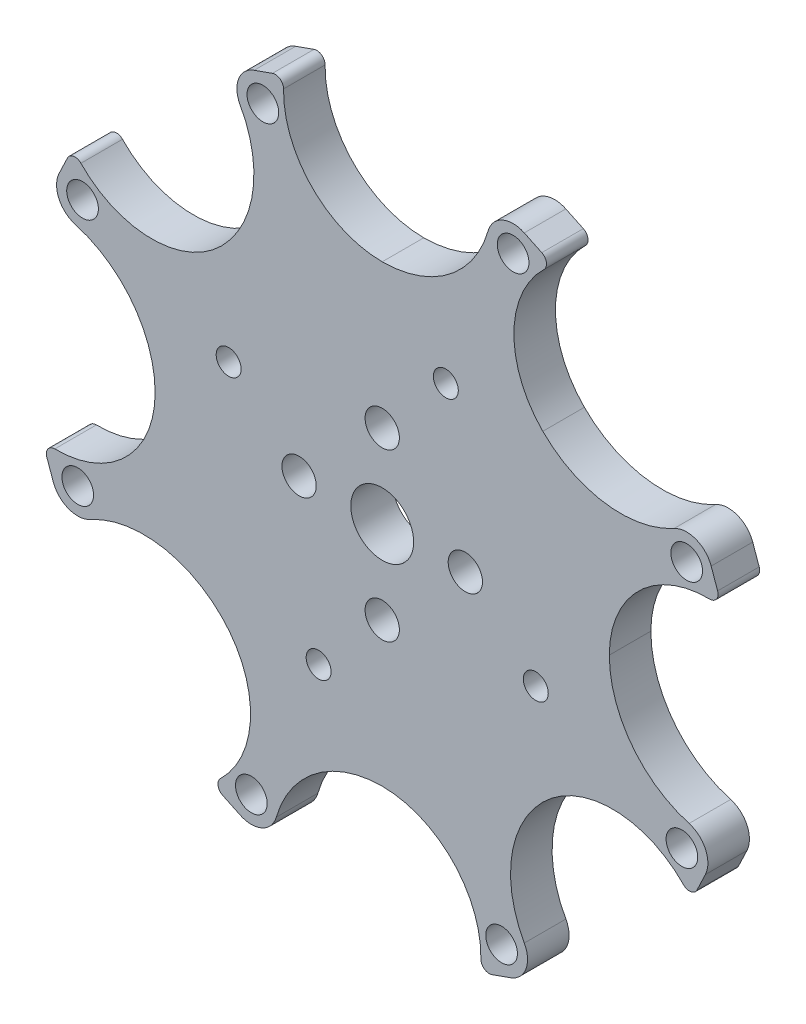
SolidWorks part; units mm, degrees
material "Thornel Mat VMA"
ref_plane "前视基准面" through (0, 0, 0) normal (0, 0, 1) x (1, 0, 0)
ref_plane "上视基准面" through (0, 0, 0) normal (0, 1, 0) x (1, 0, 0)
ref_plane "右视基准面" through (0, 0, 0) normal (1, 0, 0) x (0, 0, -1)
sketch "草图1" plane through (0, 0, 0) normal (0, 0, 1) x (1, 0, 0)
  line L0 (0, 31.3575) -> (0, 0) construction
  line L1 (0, 0) -> (22.1731, 22.1731) construction
  line L4 (0, 31.3575) -> (22.1731, 22.1731) construction
  line L6 (11.6409, 26.5357) -> (12.5976, 28.8454) construction
  line L7 (21.7656, 23.184) -> (15.5687, 29.0018) construction
  line L8 (21.7656, 23.184) -> (27.9942, 29.8184) construction
  line L9 (15.357, 30.2989) -> (13.674, 31.1018)
  line L10 (32.2836, 10.5656) -> (31.6613, 12.3233)
  line L11 (30.2989, -15.357) -> (31.1018, -13.674)
  line L12 (10.5656, -32.2836) -> (12.3233, -31.6613)
  line L13 (-15.357, -30.2989) -> (-13.674, -31.1018)
  line L14 (-32.2836, -10.5656) -> (-31.6613, -12.3233)
  line L15 (-30.2989, 15.357) -> (-31.1018, 13.674)
  line L16 (-10.5656, 32.2836) -> (-12.3233, 31.6613)
  circle A0 centre (0, 0) radius 31.3575 construction
  arc A9 (15.5687, 29.0018) -> (15.4556, 15.4556) centre (22.1731, 22.1731) ccw
  circle A11 centre (12.5976, 28.8454) radius 1.525
  circle A13 centre (0, 0) radius 40.9 construction
  arc A16 (15.5687, 29.0018) -> (15.357, 30.2989) centre (15.0125, 29.5769) ccw
  arc A17 (13.674, 31.1018) -> (10.1948, 29.5357) centre (12.5976, 28.8454) ccw
  arc A18 (0, 21.8575) -> (10.1948, 29.5357) centre (0, 32.4647) ccw
  arc A19 (31.5161, 9.4987) -> (21.8575, 0) centre (31.3575, 0) ccw
  arc A20 (31.5161, 9.4987) -> (32.2836, 10.5656) centre (31.5295, 10.2986) ccw
  arc A21 (31.6613, 12.3233) -> (28.0937, 13.6761) centre (29.3046, 11.4889) ccw
  arc A22 (15.4556, 15.4556) -> (28.0937, 13.6761) centre (22.956, 22.956) ccw
  circle A23 centre (29.3046, 11.4889) radius 1.525
  arc A24 (29.0018, -15.5687) -> (15.4556, -15.4556) centre (22.1731, -22.1731) ccw
  arc A25 (29.0018, -15.5687) -> (30.2989, -15.357) centre (29.5769, -15.0125) ccw
  arc A26 (31.1018, -13.674) -> (29.5357, -10.1948) centre (28.8454, -12.5976) ccw
  arc A27 (21.8575, 0) -> (29.5357, -10.1948) centre (32.4647, 0) ccw
  circle A28 centre (28.8454, -12.5976) radius 1.525
  arc A29 (9.4987, -31.5161) -> (0, -21.8575) centre (0, -31.3575) ccw
  arc A30 (9.4987, -31.5161) -> (10.5656, -32.2836) centre (10.2986, -31.5295) ccw
  arc A31 (12.3233, -31.6613) -> (13.6761, -28.0937) centre (11.4889, -29.3046) ccw
  arc A32 (15.4556, -15.4556) -> (13.6761, -28.0937) centre (22.956, -22.956) ccw
  circle A33 centre (11.4889, -29.3046) radius 1.525
  arc A34 (-15.5687, -29.0018) -> (-15.4556, -15.4556) centre (-22.1731, -22.1731) ccw
  arc A35 (-15.5687, -29.0018) -> (-15.357, -30.2989) centre (-15.0125, -29.5769) ccw
  arc A36 (-13.674, -31.1018) -> (-10.1948, -29.5357) centre (-12.5976, -28.8454) ccw
  arc A37 (0, -21.8575) -> (-10.1948, -29.5357) centre (0, -32.4647) ccw
  circle A38 centre (-12.5976, -28.8454) radius 1.525
  arc A39 (-31.5161, -9.4987) -> (-21.8575, 0) centre (-31.3575, 0) ccw
  arc A40 (-31.5161, -9.4987) -> (-32.2836, -10.5656) centre (-31.5295, -10.2986) ccw
  arc A41 (-31.6613, -12.3233) -> (-28.0937, -13.6761) centre (-29.3046, -11.4889) ccw
  arc A42 (-15.4556, -15.4556) -> (-28.0937, -13.6761) centre (-22.956, -22.956) ccw
  circle A43 centre (-29.3046, -11.4889) radius 1.525
  arc A44 (-29.0018, 15.5687) -> (-15.4556, 15.4556) centre (-22.1731, 22.1731) ccw
  arc A45 (-29.0018, 15.5687) -> (-30.2989, 15.357) centre (-29.5769, 15.0125) ccw
  arc A46 (-31.1018, 13.674) -> (-29.5357, 10.1948) centre (-28.8454, 12.5976) ccw
  arc A47 (-21.8575, 0) -> (-29.5357, 10.1948) centre (-32.4647, 0) ccw
  circle A48 centre (-28.8454, 12.5976) radius 1.525
  arc A49 (-9.4987, 31.5161) -> (0, 21.8575) centre (0, 31.3575) ccw
  arc A50 (-9.4987, 31.5161) -> (-10.5656, 32.2836) centre (-10.2986, 31.5295) ccw
  arc A51 (-12.3233, 31.6613) -> (-13.6761, 28.0937) centre (-11.4889, 29.3046) ccw
  arc A52 (-15.4556, 15.4556) -> (-13.6761, 28.0937) centre (-22.956, 22.956) ccw
  circle A53 centre (-11.4889, 29.3046) radius 1.525
  circle A54 centre (0, 0) radius 3.025
  circle A55 centre (0, 0) radius 8 construction
  circle A56 centre (-8, 0) radius 1.65
  circle A57 centre (0, 8) radius 1.65
  circle A58 centre (8, 0) radius 1.65
  circle A59 centre (0, -8) radius 1.65
  point P98 (0, 0)
  point P102 (0, 0)
  dimension "D1" = 9.5
  dimension "D3" = 45
  dimension "D4" = 3.05
  dimension "D5" = 9.1
  dimension "D8" = 81.8
  dimension "D9" = 9.5
  dimension "D10" = 2.5
  dimension "D11" = 0.8
  dimension "D13" = 6.05
  dimension "D14" = 16
  dimension "D15" = 3.3
  dimension "D2" = 24
  dimension "D6" = 11.4
  dimension "D7" = 2.5
  dimension "D17" = 8.5
  dimension "D12" = 8
  dimension "D16" = 4
extrude "凸台-拉伸1" add sketch "草图1" along normal blind 4
sketch "草图2" plane through (0, 0, 4) normal (0, 0, 1) x (1, 0, 0)
  line L0 (-22.1731, -22.1731) -> (0, -31.3575) construction
  line L1 (-11.0866, -26.7653) -> (0, 0) construction
  circle A0 centre (0, 0) radius 16 construction
  circle A1 centre (-6.1229, -14.7821) radius 1.2
  circle A3 centre (-14.7821, 6.1229) radius 1.2
  circle A4 centre (6.1229, 14.7821) radius 1.2
  circle A5 centre (14.7821, -6.1229) radius 1.2
  point P19 (0, 0)
  dimension "D1" = 32
  dimension "D2" = 2.4
  dimension "D3" = 4
extrude "切除-拉伸1" cut sketch "草图2" against normal blind 10
cosmetic thread "装饰螺纹线1" parameters "D2"=3
cosmetic thread "装饰螺纹线2" parameters "D2"=3
cosmetic thread "装饰螺纹线3" parameters "D2"=3
cosmetic thread "装饰螺纹线4" parameters "D2"=3
